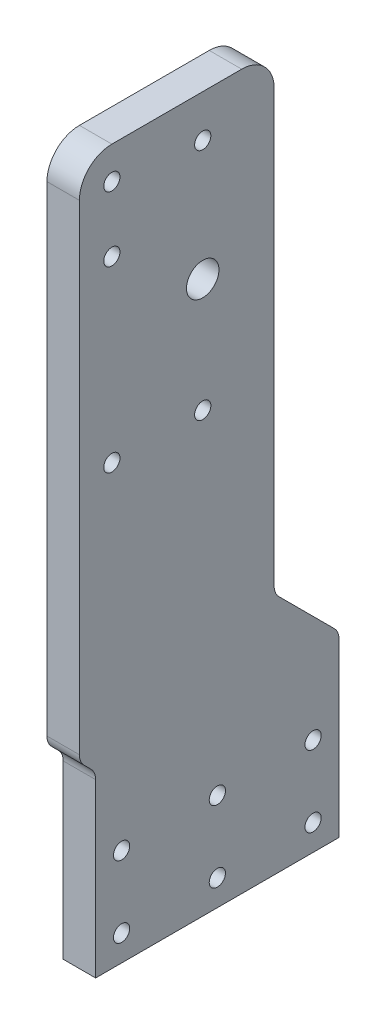
SolidWorks part; units mm, degrees
ref_plane "Front Plane" through (0, 0, 0) normal (0, 0, 1) x (1, 0, 0)
ref_plane "Top Plane" through (0, 0, 0) normal (0, 1, 0) x (1, 0, 0)
ref_plane "Right Plane" through (0, 0, 0) normal (1, 0, 0) x (0, 0, -1)
sketch "Sketch1" plane through (0, 0, 0) normal (1, 0, 0) x (0, 0, -1)
  line L0 (0, 0) -> (75, 0)
  line L1 (75, 0) -> (75, 52.9289)
  line L2 (73.5355, 56.4645) -> (56.4645, 73.5355)
  line L3 (55, 77.0711) -> (55, 210)
  line L4 (45, 220) -> (5, 220)
  line L5 (-5, 210) -> (-5, 62.0711)
  line L6 (-3.5355, 58.5355) -> (-1.4645, 56.4645)
  line L7 (0, 52.9289) -> (0, 0)
  circle A0 centre (5, 210) radius 2.5
  circle A1 centre (5, 190) radius 2.5
  circle A2 centre (33, 207) radius 2.5
  circle A3 centre (5, 135) radius 2.5
  circle A4 centre (33, 135) radius 2.5
  circle A5 centre (8, 30) radius 2.5
  circle A6 centre (8, 8) radius 2.5
  circle A7 centre (37.5, 8) radius 2.5
  circle A8 centre (37.5, 30) radius 2.5
  circle A9 centre (67, 30) radius 2.5
  circle A10 centre (67, 8) radius 2.5
  circle A11 centre (33, 170) radius 5
  arc A12 (75, 52.9289) -> (73.5355, 56.4645) centre (70, 52.9289) ccw
  arc A13 (0, 52.9289) -> (-1.4645, 56.4645) centre (-5, 52.9289) ccw
  arc A14 (-3.5355, 58.5355) -> (-5, 62.0711) centre (0, 62.0711) cw
  arc A15 (56.4645, 73.5355) -> (55, 77.0711) centre (60, 77.0711) cw
  arc A16 (55, 210) -> (45, 220) centre (45, 210) ccw
  arc A17 (5, 220) -> (-5, 210) centre (5, 210) ccw
  point P31 (0, 0)
  point P32 (0, 0)
  point P33 (0, 0)
  point P34 (0, 0)
  point P37 (0, 0)
  point P38 (0, 0)
  point P39 (0, 0)
  point P40 (37.5, 0)
  point P41 (0, 0)
  point P42 (0, 0)
  point P45 (75, 55)
  point P48 (0, 55)
  point P51 (-5, 60)
  dimension "D8" = 5
  dimension "D9" = 5
  dimension "D10" = 5
  dimension "D11" = 5
  dimension "D12" = 5
  dimension "D13" = 5
  dimension "D14" = 5
  dimension "D15" = 5
  dimension "D16" = 5
  dimension "D17" = 5
  dimension "D18" = 5
  dimension "D25" = 10
  dimension "D33" = 5
  dimension "D34" = 5
  dimension "D35" = 5
  dimension "D36" = 5
  dimension "D37" = 10
  dimension "D1" = 60
  dimension "D2" = 75
  dimension "D3" = 55
  dimension "D4" = 55
  dimension "D5" = 5
  dimension "D6" = 5
  dimension "D7" = 220
  dimension "D19" = 10
  dimension "D20" = 10
  dimension "D21" = 20
  dimension "D22" = 75
  dimension "D23" = 72
  dimension "D24" = 28
  dimension "D26" = 35
  dimension "D27" = 8
  dimension "D28" = 8
  dimension "D29" = 30
  dimension "D30" = 30
  dimension "D31" = 8
  dimension "D32" = 8
extrude "Boss-Extrude1" add sketch "Sketch1" along normal blind 10
